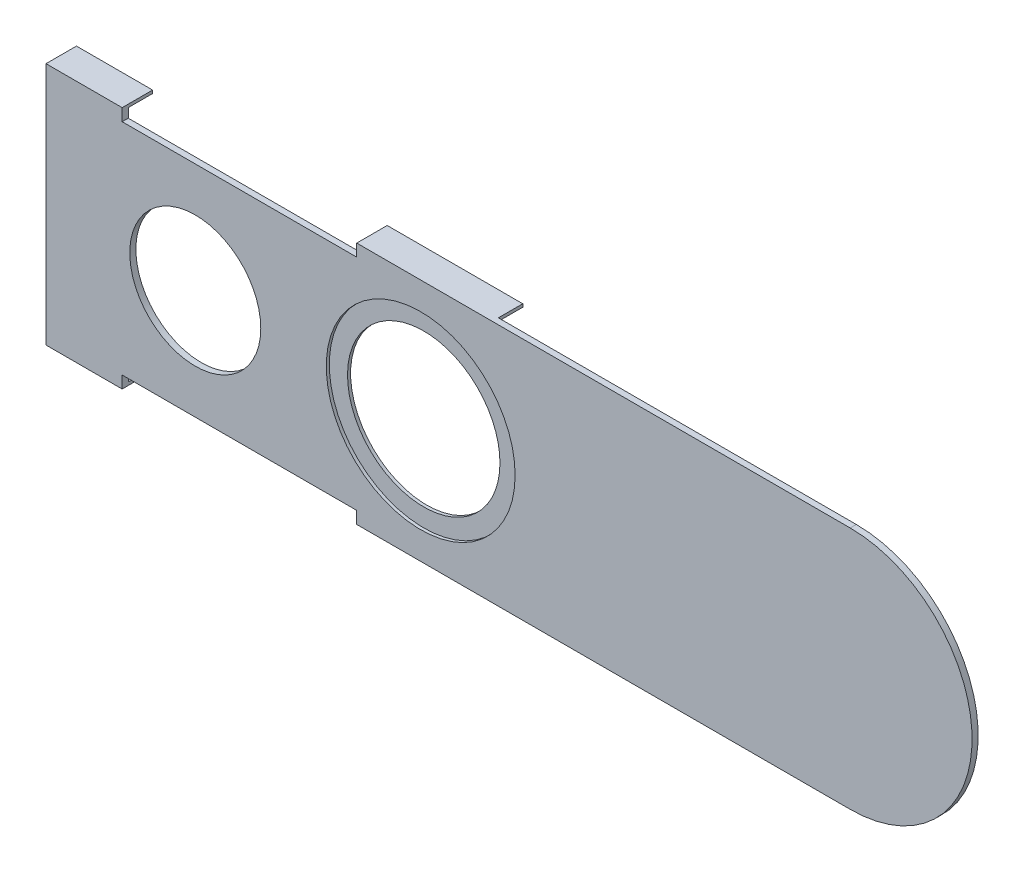
SolidWorks part; units mm, degrees
material "Nickel"
ref_plane "Front Plane" through (0, 0, 0) normal (0, 0, 1) x (1, 0, 0)
ref_plane "Top Plane" through (0, 0, 0) normal (0, 1, 0) x (1, 0, 0)
ref_plane "Right Plane" through (0, 0, 0) normal (1, 0, 0) x (0, 0, -1)
sketch "Sketch1" plane through (0, 0, 0) normal (0, 0, 1) x (1, 0, 0)
  line L0 (0, -10.16) -> (-67.056, -10.16)
  line L1 (-67.056, -10.16) -> (-67.056, 10.16)
  line L2 (-67.056, 10.16) -> (0, 10.16)
  line L3 (10.16, 0) -> (10.16, 15.0411)
  arc A0 (0, -10.16) -> (0, 10.16) centre (0, 0) ccw
  dimension "D1" = 20.32
  dimension "D2" = 77.216
extrude "Boss-Extrude1" add sketch "Sketch1" along normal blind 0.508 contours A0 L2 L1 L0
sketch "Sketch2" plane through (0, 0, 0.508) normal (0, 0, 1) x (1, 0, 0)
  circle A0 centre (-54.61, 0) radius 7.874
  circle A1 centre (-35.814, 0) radius 6.35
  point P2 (0, 0)
  dimension "D2" = 15.748
  dimension "D3" = 12.7
extrude "Cut-Extrude2" cut sketch "Sketch2" against normal blind 0.254
sketch "Sketch5" plane through (0, 0, 0.254) normal (0, 0, 1) x (1, 0, 0)
  circle A0 centre (-35.814, 0) radius 6.3542
extrude "Cut-Extrude3" cut sketch "Sketch5" against normal through all
sketch "Sketch6" plane through (0, 0, 0.254) normal (0, 0, 1) x (1, 0, 0)
  circle A0 centre (-54.61, 0) radius 5.461
  dimension "D1" = 10.922
extrude "Cut-Extrude4" cut sketch "Sketch6" against normal through all
sketch "Sketch7" plane through (0, 0, 0) normal (0, 0, -1) x (-1, 0, 0)
  line L0 (67.056, 10.16) -> (60.706, 10.16)
  line L1 (67.056, 10.16) -> (0, 10.16) construction
  line L2 (60.706, 9.144) -> (60.706, -9.144)
  line L3 (67.056, 10.16) -> (67.056, -10.16) construction
  line L4 (67.056, -10.16) -> (67.056, 10.16) construction
  line L5 (60.706, 10.16) -> (60.706, 9.144)
  line L6 (60.706, -9.144) -> (41.148, -9.144)
  line L7 (60.706, 9.144) -> (41.148, 9.144)
  line L8 (41.148, 9.144) -> (41.148, -9.144)
  line L9 (41.148, 9.144) -> (41.148, 10.16)
  line L10 (41.148, 10.16) -> (60.706, 10.16)
  line L11 (60.706, -9.144) -> (60.706, -10.16)
  line L12 (0, -10.16) -> (67.056, -10.16) construction
  line L13 (60.706, -10.16) -> (41.148, -10.16)
  line L14 (41.148, -10.16) -> (41.148, -9.144)
  point P8 (60.706, 0)
  point P11 (67.056, 0)
  line M9 (0, -10.16) -> (67.056, -10.16)
  line M11 (67.056, 10.16) -> (0, 10.16)
  dimension "D1" = 6.35
  dimension "D2" = 18.288
  dimension "D3" = 19.558
extrude "Cut-Extrude5" cut sketch "Sketch7" against normal through all contours L9 L7 L5 M11 | L14 L11 L6 M9
sketch "Sketch8" plane through (0, 0, 0) normal (0, 0, -1) x (-1, 0, 0)
  line L0 (67.056, -10.16) -> (67.056, 10.16) construction
  line L1 (60.706, 10.16) -> (67.056, 10.16)
  line L2 (60.706, 10.16) -> (60.706, 9.906)
  line L3 (60.706, 9.906) -> (67.056, 9.906)
  line L4 (67.056, 10.16) -> (67.056, 9.906)
  dimension "D1" = 0.254
extrude "Boss-Extrude2" add sketch "Sketch8" along normal blind 2.032
sketch "Sketch10" plane through (0, 0, 0) normal (0, 0, -1) x (-1, 0, 0)
  line L1 (41.148, 10.16) -> (29.8448, 10.16)
  line L2 (41.148, 10.16) -> (41.148, 9.906)
  line L3 (41.148, 9.906) -> (29.8448, 9.906)
  line L4 (29.8448, 10.16) -> (29.8448, 9.906)
  dimension "D1" = 0.254
extrude "Boss-Extrude3" add sketch "Sketch10" along normal blind 2.032
sketch "Sketch11" plane through (0, 0, 0) normal (0, 0, -1) x (-1, 0, 0)
  line L0 (60.706, -9.144) -> (60.706, -10.16) construction
  line L1 (67.056, -10.16) -> (60.706, -10.16)
  line L2 (67.056, -10.16) -> (67.056, -9.906)
  line L3 (67.056, -9.906) -> (60.706, -9.906)
  line L4 (60.706, -10.16) -> (60.706, -9.906)
  dimension "D1" = 0.254
extrude "Boss-Extrude4" add sketch "Sketch11" along normal blind 2.032
sketch "Sketch12" plane through (0, 0, 0) normal (0, 0, -1) x (-1, 0, 0)
  line L1 (41.148, -10.16) -> (29.21, -10.16)
  line L2 (41.148, -10.16) -> (41.148, -9.906)
  line L3 (41.148, -9.906) -> (29.21, -9.906)
  line L4 (29.21, -10.16) -> (29.21, -9.906)
  dimension "D1" = 0.254
  dimension "D2" = 11.938
extrude "Boss-Extrude5" add sketch "Sketch12" along normal blind 2.032
sketch "Sketch13" plane through (0, 0, 0.508) normal (0, 0, 1) x (1, 0, 0)
  circle A0 centre (-35.814, 0) radius 7.874
  dimension "D1" = 15.748
extrude "Cut-Extrude7" cut sketch "Sketch13" against normal blind 0.254
sketch "Sketch14" plane through (0, 0, 0.508) normal (0, 0, 1) x (1, 0, 0)
  circle A0 centre (-54.61, 0) radius 7.874
  circle A1 centre (-54.61, 0) radius 5.461
extrude "Boss-Extrude8" add sketch "Sketch14" against normal blind 0.254
